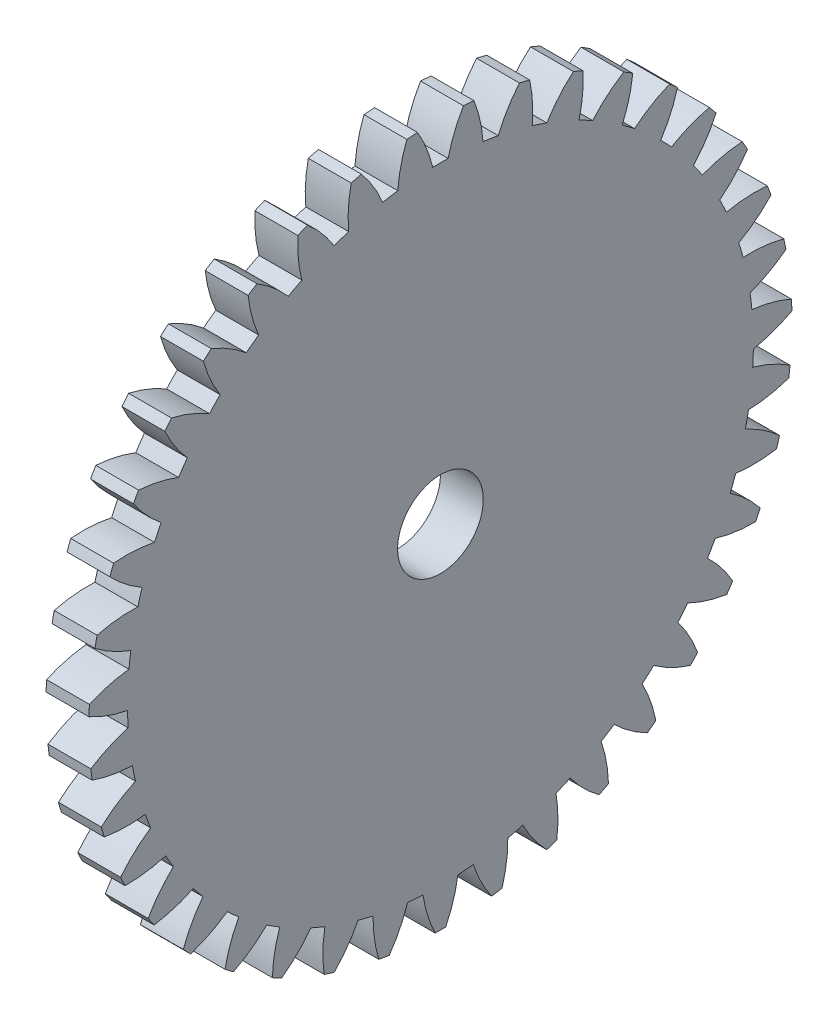
SolidWorks part; units mm, degrees
ref_plane "Plane1" through (0, 0, 0) normal (0, 0, 1) x (1, 0, 0)
ref_plane "Plane2" through (0, 0, 0) normal (0, 1, 0) x (1, 0, 0)
ref_plane "Plane3" through (0, 0, 0) normal (1, 0, 0) x (0, 0, -1)
sketch "HoldingSke" plane through (0, 0, 0) normal (0, 1, 0) x (1, 0, 0)
  line L0 (0, 0) -> (1.9429, -1.5733)
  line L1 (-15, 0) -> (100, 0) construction
  line L2 (0, 0) -> (-2.1039, 2.3779)
  line L3 (0, 0) -> (-11.863, 4.5341)
  line L4 (0, 0) -> (6.7114, 5.4348)
  line L5 (0, 0) -> (-46.8476, -17.4728)
  line L6 (0, 0) -> (-0.829, -0.5593)
  line L7 (-2.1039, 2.3779) -> (8.6586, 51.2059)
  line L8 (-76.2, 54.61) -> (-75.9, 54.61)
  line L9 (-71.009, 38.7566) -> (-53.1078, 45.2721)
  line L10 (-76.2, 71.12) -> (104.1128, 71.12)
  line L11 (0, 0) -> (-1, 0)
  line L12 (-76.2, 101.6) -> (-76.185, 101.6)
  line L13 (24.9733, 27.94) -> (52.9518, 28.4284)
  line L14 (24.9733, 27.94) -> (24.9743, 27.94)
  line L15 (24.9733, 27.94) -> (100.4006, 29.5858)
  line L16 (-63.627, -0.4) -> (-12.827, -0.4)
  circle A0 centre (0, 0) radius 1
  circle A1 centre (0, 0) radius 7.299
  circle A2 centre (0, 0) radius 37.5
  circle A3 centre (0, 0) radius 1
  dimension "MHD" = 14.598
  dimension "Hub_dia" = 75
  dimension "Bore" = 2
  dimension "MBD" = 2
  dimension "Num_teeth" = 39
  dimension "Pitch" = 2.5
  dimension "Overall_len" = 50
  dimension "Show_teeth" = 39
  dimension "Thickness" = 1
  dimension "OAL" = 50.0001
  dimension "T_dim" = 0.3
  dimension "Ap" = 20
  dimension "H" = 19.05
  dimension "Pitch_radius" = 180.3128
  dimension "Width" = 1
  dimension "Backlash" = 0.015
  dimension "Addendum_fac" = 1
  dimension "Dedendum_fac" = 1.25
  dimension "Clearance_fac" = 0.25
  dimension "Dedendum_add" = 0.001
  dimension "Module" = 0.4
sketch "BasProSke" plane through (0, 0, 0) normal (0, 1, 0) x (1, 0, 0)
  line L0 (-10, 0) -> (60, 0) construction
  line L1 (0, 0) -> (0, 8.2)
  line L2 (0, 0) -> (1, 0)
  line L3 (1, 0) -> (1, 8.2)
  line L4 (1, 8.2) -> (0, 8.2)
  dimension "Thickness" = 1
  dimension "Diameter" = 16.4
revolve "Base-Revolve" add sketch "BasProSke" angle 360 about L0
sketch "TooCutSke" plane through (0, 0, 0) normal (1, 0, 0) x (0, 0, -1)
  line L1 (0, 0) -> (0, 107) construction
  line L2 (0, 0) -> (-0.3403, 7.7926) construction
  line L3 (0, 0) -> (-1.2544, 15.5388) construction
  line L4 (-0.3403, 7.7926) -> (-0.6272, 7.7694) construction
  arc A0 (0.1796, 7.2968) -> (-0.1796, 7.2968) centre (0, 0) ccw
  arc A1 (0.5517, 8.2069) -> (-0.5517, 8.2069) centre (0, 0) ccw
  circle A2 centre (0, 0) radius 7.8 construction
  circle A3 centre (0, 0) radius 7.3296 construction
  arc A4 (-0.1796, 7.2968) -> (-0.5517, 8.2069) centre (-3.2174, 6.5857) ccw
  arc A5 (0.5517, 8.2069) -> (0.1796, 7.2968) centre (3.2174, 6.5857) ccw
  dimension "Root_dia" = 14.598
  dimension "Overcut_dia" = 16.4508
  dimension "Pitch_dia" = 15.6
  dimension "Base_dia" = 14.6592
  dimension "Flank_rad" = 3.12
  dimension "Half_ang" = 4.615
  dimension "Half_CT" = 0.2878
extrude "ToothCut" cut sketch "TooCutSke" along normal through all
fillet "Breaks" [suppressed] radius 0.008
fillet "RootFillets" [suppressed] radius 0.101
pattern_circular "TeethCuts" count 39 every 9.231 about axis through (-10, 0, 0) along (1, 0, 0) of "ToothCut", "RootFillets", "Breaks"
sketch "HubNeaOneSke" plane through (0, 0, 0) normal (-1, 0, 0) x (0, 0, 1)
  circle A0 centre (0, 0) radius 7.299
  dimension "Diameter" = 14.598
extrude "HubNearOne" [suppressed] add sketch "HubNeaOneSke" along normal blind 49.0001
sketch "HubNeaBotSke" plane through (0, 0, 0) normal (-1, 0, 0) x (0, 0, 1)
  circle A0 centre (0, 0) radius 7.299
  dimension "Diameter" = 14.598
extrude "HubNearBoth" [suppressed] add sketch "HubNeaBotSke" along normal blind 24.5
ref_plane "FarPln" through (1, 0, 0) normal (1, 0, 0) x (0, 0, -1)
sketch "HubFarSke" plane through (1, 0, 0) normal (1, 0, 0) x (0, 0, -1)
  circle A0 centre (0, 0) radius 7.299
  dimension "Diameter" = 14.598
extrude "HubFar" [suppressed] add sketch "HubFarSke" along normal blind 24.5
sketch "BorSke" plane through (0, 0, 0) normal (1, 0, 0) x (0, 0, -1)
  circle A0 centre (0, 0) radius 1
  dimension "Diameter" = 2
extrude "Bore" cut sketch "BorSke" along normal mid plane 100.0001
sketch "KeySke" plane through (0, 0, 0) normal (1, 0, 0) x (0, 0, -1)
  line L0 (-0.4, 0) -> (-0.4, 1.3)
  line L1 (-0.4, 1.3) -> (0.4, 1.3)
  line L2 (0.4, 1.3) -> (0.4, 0)
  line L3 (0, 0) -> (0, 34) construction
  line L4 (-0.4, 0) -> (0.4, 0)
  dimension "Offset" = 1.3
  dimension "Width" = 0.8
extrude "Keyway" [suppressed] cut sketch "KeySke" along normal mid plane 100.0001
pattern_circular "Keyway2" [suppressed] count 2 every 90 about axis through (-10, 0, 0) along (1, 0, 0)
equation "' \"Module@HoldingSke\" = 6.35"
equation "' \"Num_teeth@HoldingSke\" = 12"
equation "' \"Ap@HoldingSke\" =  20"
equation "' \"Ap@HoldingSke\" = 20"
equation "' \"Width@HoldingSke\" = 0.5 * 25.4"
equation "' \"Hub_dia@HoldingSke\"= 1 * 25.4"
equation "' \"Hub_dia@HoldingSke\" = 1 * 25.4"
equation "' \"Overall_len@HoldingSke\" = 1.0 * 25.4"
equation "' \"Bore@HoldingSke\" = 0.75 * 25.4"
equation "' \"T_dim@HoldingSke\" = 0.1 * 25.4"
equation "' \"Width@KeySke\" = 0.25 * 25.4"
equation "' \"Show_teeth@HoldingSke\" = 13"
equation "' \"Backlash@HoldingSke\" = 0.009 * 25.4"
equation "' \"Addendum_fac@HoldingSke\" = 1.0"
equation "' \"Dedendum_fac@HoldingSke\" = 1.25"
equation "' \"Dedendum_add@HoldingSke\" = 0.00005 * 25.4"
equation "' \"Clearance_fac@HoldingSke\" = 0.25"
equation "\"Pitch@HoldingSke\" = 1 / \"Module@HoldingSke\""
equation "\"Overcut_dia@TooCutSke\" = (\"Num_teeth@HoldingSke\" + 2 * \"Addendum_fac@HoldingSke\") / \"Pitch@HoldingSke\" + 0.002 * 25.4"
equation "\"Pitch_dia@TooCutSke\" = \"Num_teeth@HoldingSke\" / \"Pitch@HoldingSke\""
equation "\"Base_dia@TooCutSke\" = \"Num_teeth@HoldingSke\" / \"Pitch@HoldingSke\" * cos((\"Ap@HoldingSke\"  * 3.14159265 / 180))"
equation "\"Root_dia@TooCutSke\" = (\"Num_teeth@HoldingSke\" + 2) / \"Pitch@HoldingSke\" - 2 * (\"Addendum_fac@HoldingSke\" + \"Dedendum_fac@HoldingSke\") / \"Pitch@HoldingSke\" - \"Dedendum_add@HoldingSke\" * 2"
equation "\"Half_ang@TooCutSke\" = 180 / \"Num_teeth@HoldingSke\""
equation "\"Half_CT@TooCutSke\" = \"Num_teeth@HoldingSke\" / \"Pitch@HoldingSke\" * sin((3.14159265 / 2 / \"Num_teeth@HoldingSke\")) / 2 - 7 * \"Backlash@HoldingSke\" / 4"
equation "\"Flank_rad@TooCutSke\" = \"Num_teeth@HoldingSke\" / \"Pitch@HoldingSke\" / 5"
equation "\"Radius@RootFillets\" = \"Clearance_fac@HoldingSke\" / \"Pitch@HoldingSke\" + \"Dedendum_add@HoldingSke\""
equation "\"Break_rad@Breaks\" = 0.02 / \"Pitch@HoldingSke\""
equation "\"Thickness@HoldingSke\" = \"Width@HoldingSke\""
equation "\"OAL@HoldingSke\" = \"Thickness@HoldingSke\""
equation "\"MHD@HoldingSke\" = (\"Num_teeth@HoldingSke\" + 2) / \"Pitch@HoldingSke\" - 2 * (\"Addendum_fac@HoldingSke\" + \"Dedendum_fac@HoldingSke\")  / \"Pitch@HoldingSke\" - \"Dedendum_add@HoldingSke\" * 2"
equation "\"MBD@HoldingSke\" = (\"Num_teeth@HoldingSke\" + 2) / \"Pitch@HoldingSke\" - 2 * (\"Addendum_fac@HoldingSke\" + \"Dedendum_fac@HoldingSke\")  / \"Pitch@HoldingSke\" - \"Dedendum_add@HoldingSke\" * 2 - 0.002 * 25.4"
equation "\"MHD@HoldingSke\" = ((sgn( \"MHD@HoldingSke\" - \"Hub_dia@HoldingSke\" )-1)*( \"MHD@HoldingSke\" - \"Hub_dia@HoldingSke\" ))/-2+ \"Hub_dia@HoldingSke\""
equation "\"MBD@HoldingSke\" = ((sgn( \"MBD@HoldingSke\" - \"Bore@HoldingSke\" )-1)*( \"MBD@HoldingSke\" - \"Bore@HoldingSke\" ))/-2+ \"Bore@HoldingSke\""
equation "\"OAL@HoldingSke\" = ((sgn( \"OAL@HoldingSke\" - \"Overall_len@HoldingSke\" )+1)*( \"OAL@HoldingSke\" - \"Overall_len@HoldingSke\" ))/2 + \"Overall_len@HoldingSke\" + 0.000002 * 25.4"
equation "\"Num_teeth@TeethCuts\" = int( \"Show_teeth@HoldingSke\" ) + 1"
equation "\"Num_teeth@TeethCuts\" = ((sgn( \"Num_teeth@TeethCuts\" - \"Num_teeth@HoldingSke\" )-1)*( \"Num_teeth@TeethCuts\" - \"Num_teeth@HoldingSke\" ))/-2+ \"Num_teeth@HoldingSke\""
equation "\"Num_teeth@TeethCuts\" = ((sgn( \"Num_teeth@TeethCuts\" - 2.0)+1)*( \"Num_teeth@TeethCuts\" - 2.0))/2 +2.0"
equation "\"Angle@TeethCuts\" = 360.0 / \"Num_teeth@HoldingSke\""
equation "\"Diameter@BasProSke\" = (\"Num_teeth@HoldingSke\" + 2 * \"Addendum_fac@HoldingSke\") / \"Pitch@HoldingSke\""
equation "\"Thickness@BasProSke\"  = \"Thickness@HoldingSke\""
equation "' \"Fillet_rad@BasProSke\" =  \"Thickness@HoldingSke\" * 0.05"
equation "' \"Fillet_rad@BasProSke\" = \"Thickness@HoldingSke\" * 0.05"
equation "\"MHD@HoldingSke\" = ((sgn( \"MHD@HoldingSke\" - \"Root_dia@TooCutSke\" )-1)*( \"MHD@HoldingSke\" - \"Root_dia@TooCutSke\" ))/-2+ \"Root_dia@TooCutSke\""
equation "\"Diameter@HubNeaOneSke\" = \"MHD@HoldingSke\""
equation "\"Length@HubNearOne\" = \"OAL@HoldingSke\" - \"Thickness@BasProSke\""
equation "\"Diameter@HubNeaBotSke\" = \"MHD@HoldingSke\""
equation "\"Length@HubNearBoth\" = ( \"OAL@HoldingSke\" - \"Thickness@BasProSke\" ) / 2.0"
equation "\"Thickness@FarPln\" = \"Thickness@BasProSke\""
equation "\"Diameter@HubFarSke\" = \"MHD@HoldingSke\""
equation "\"Length@HubFar\" = ( \"OAL@HoldingSke\" - \"Thickness@BasProSke\" ) / 2.0"
equation "\"Diameter@BorSke\" = \"MBD@HoldingSke\""
equation "\"D1@Bore\" = \"OAL@HoldingSke\" * 2.0"
equation "\"D1@Keyway\" = \"OAL@HoldingSke\" * 2.0"
equation "\"Offset@KeySke\" = \"T_dim@HoldingSke\" + \"MBD@HoldingSke\" / 2.0"
